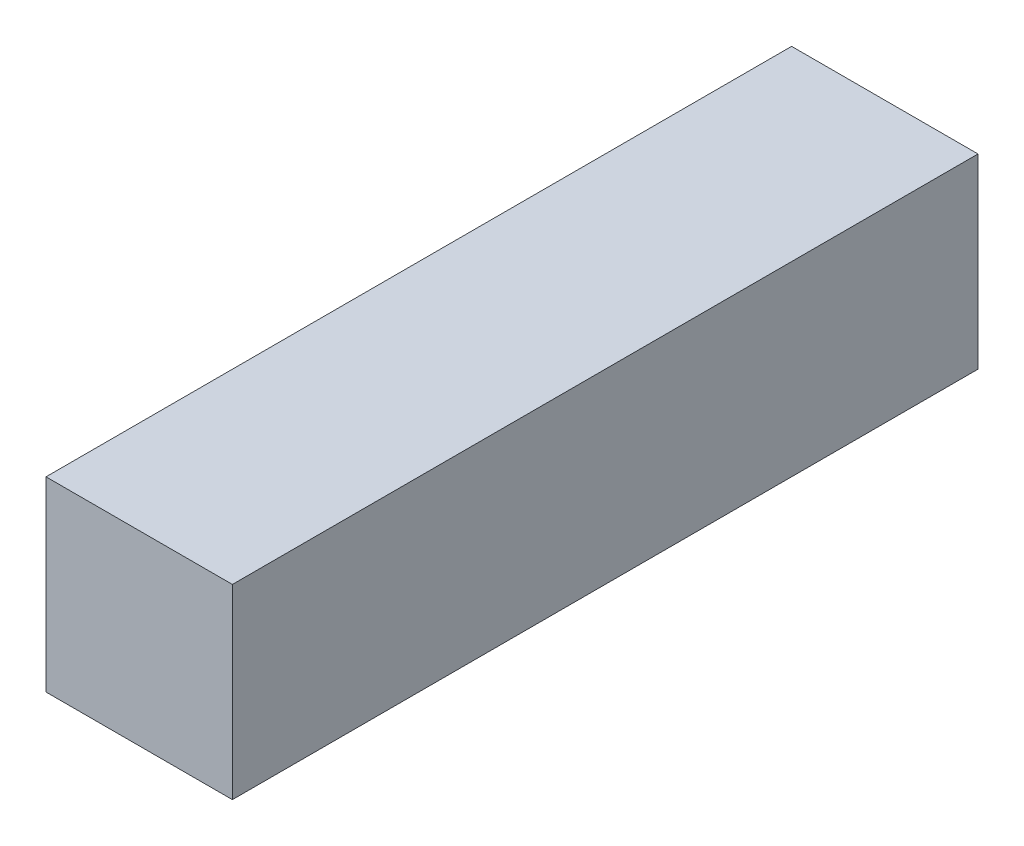
SolidWorks part; units mm, degrees
ref_plane "Front Plane" through (0, 0, 0) normal (0, 0, 1) x (1, 0, 0)
ref_plane "Top Plane" through (0, 0, 0) normal (0, 1, 0) x (1, 0, 0)
ref_plane "Right Plane" through (0, 0, 0) normal (1, 0, 0) x (0, 0, -1)
sketch "Sketch2" plane through (0, 0, 0) normal (0, 0, 1) x (1, 0, 0)
  line L1 (0, 0) -> (3, 0)
  line L2 (0, 0) -> (0, -3)
  line L3 (0, -3) -> (3, -3)
  line L4 (3, 0) -> (3, -3)
  dimension "D1" = 3
  dimension "D2" = 3
extrude "Boss-Extrude1" add sketch "Sketch2" along normal blind 12
